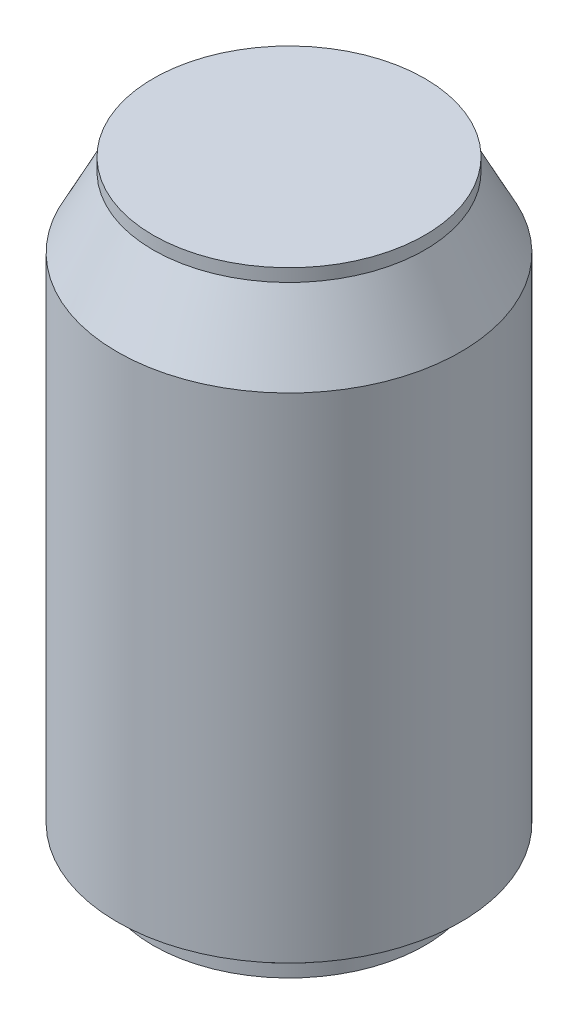
SolidWorks part; units mm, degrees
ref_plane "Front Plane" through (0, 0, 0) normal (0, 0, 1) x (1, 0, 0)
ref_plane "Top Plane" through (0, 0, 0) normal (0, 1, 0) x (1, 0, 0)
ref_plane "Right Plane" through (0, 0, 0) normal (1, 0, 0) x (0, 0, -1)
sketch "Sketch1" plane through (0, 0, 0) normal (0, 0, 1) x (1, 0, 0)
  line L0 (0, 0) -> (0, 122.2375)
  line L1 (0, 122.2375) -> (26.9875, 122.2375)
  line L2 (26.9875, 122.2375) -> (26.9875, 119.6975)
  line L3 (26.9875, 119.6975) -> (34.1313, 105.7275)
  line L4 (34.1313, 105.7275) -> (34.1313, 7.62)
  line L5 (34.1313, 7.62) -> (26.9875, 2.54)
  line L6 (26.9875, 2.54) -> (26.9875, 0)
  line L7 (26.9875, 0) -> (0, 0)
  dimension "D1" = 34.1313
  dimension "D2" = 122.2375
  dimension "D3" = 26.9875
  dimension "D4" = 2.54
  dimension "D5" = 7.62
  dimension "D6" = 16.51
revolve "Revolve1" add sketch "Sketch1" angle 360 about L0
ref_plane "Plane1" through (-34.1313, 0, 0) normal (-1, 0, 0) x (0, 0, 1)
sketch "Sketch2" plane through (-34.1313, 0, 0) normal (-1, 0, 0) x (0, 0, 1)
  line L0 (-34.1313, 7.62) -> (34.1313, 7.62) construction
  line L1 (9.525, 26.67) -> (-9.525, 26.67)
  line L2 (9.525, 26.67) -> (9.525, 7.62)
  line L3 (9.525, 7.62) -> (-9.525, 7.62)
  line L4 (-9.525, 26.67) -> (-9.525, 7.62)
  point P6 (0, 7.62)
  dimension "D1" = 19.05
extrude "Boss-Extrude1" add sketch "Sketch2" against normal blind 7.62
sketch "Sketch3" plane through (0, 0, 0) normal (0, -1, 0) x (1, 0, 0)
  line L1 (0, 0) -> (12.7, 0)
  line L2 (0, 0) -> (0, 12.7)
  line L3 (0, 12.7) -> (12.7, 12.7)
  line L4 (12.7, 0) -> (12.7, 12.7)
  dimension "D1" = 12.7
extrude "Cut-Extrude1" cut sketch "Sketch3" against normal blind 25.4
